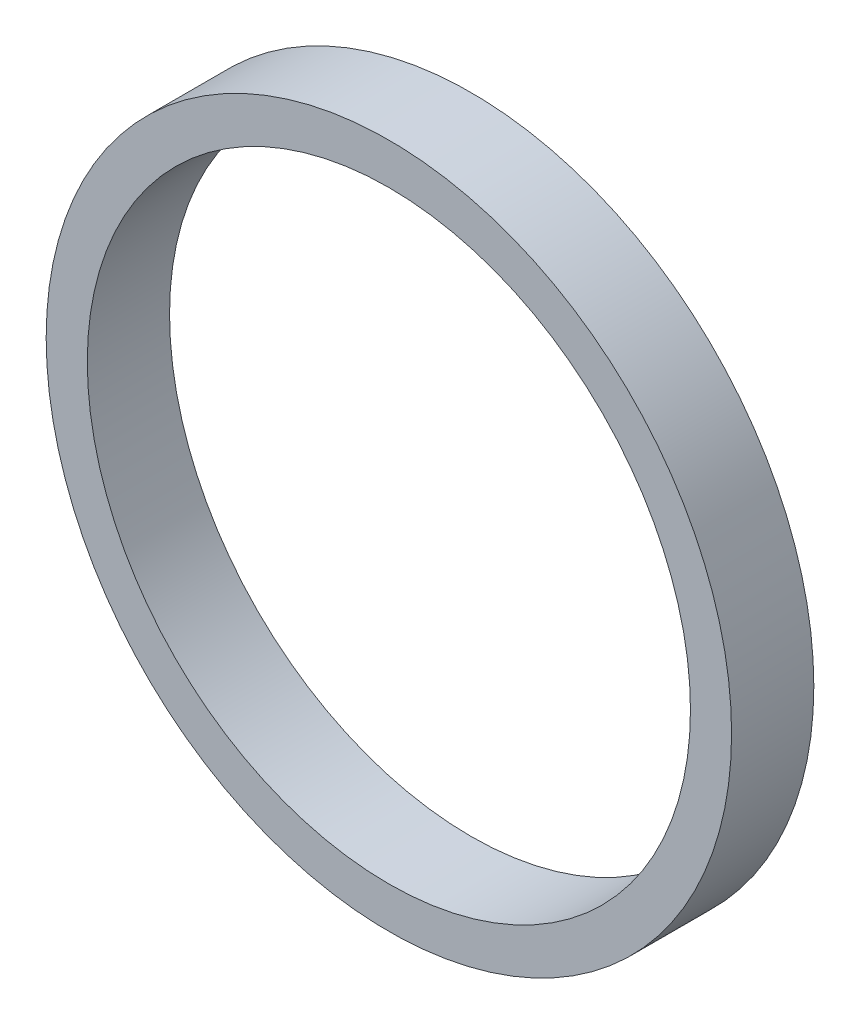
SolidWorks part; units mm, degrees
material "Rubber"
ref_plane "Front Plane" through (0, 0, 0) normal (0, 0, 1) x (1, 0, 0)
ref_plane "Top Plane" through (0, 0, 0) normal (0, 1, 0) x (1, 0, 0)
ref_plane "Right Plane" through (0, 0, 0) normal (1, 0, 0) x (0, 0, -1)
sketch "Sketch1" plane through (0, 0, 0) normal (0, 0, 1) x (1, 0, 0)
  circle A0 centre (0, 0) radius 5.5
  circle A1 centre (0, 0) radius 6.25
  dimension "D1" = 11
  dimension "D2" = 12.5
extrude "Boss-Extrude1" add sketch "Sketch1" along normal blind 1.5
